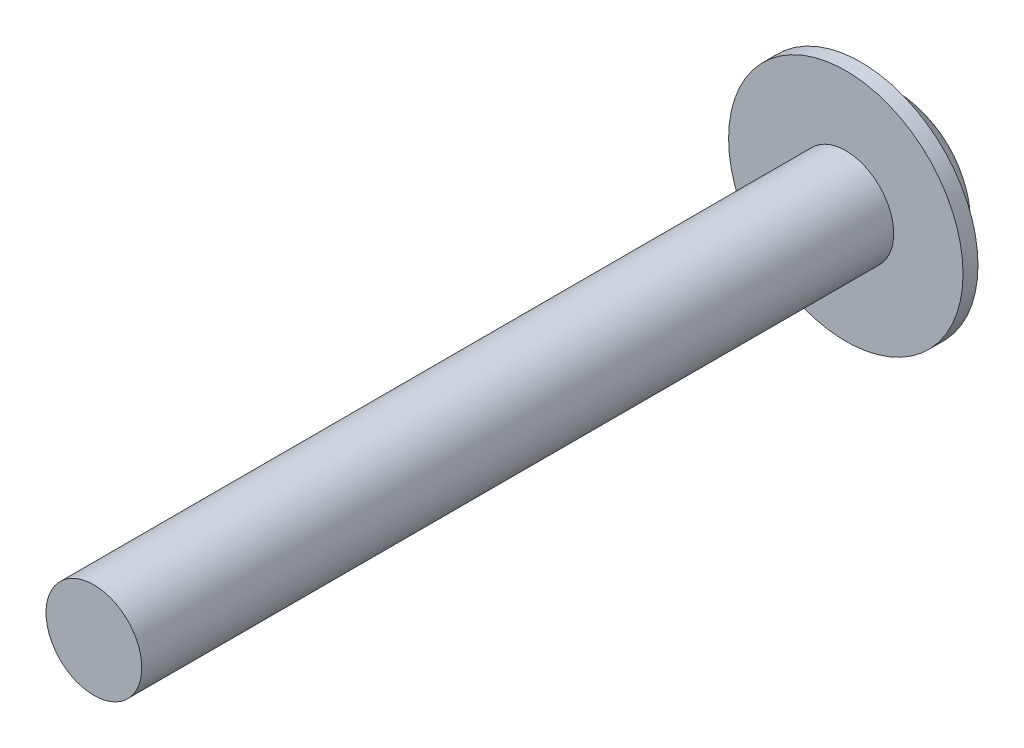
SolidWorks part; units mm, degrees
material "Chrome Stainless Steel"
ref_plane "Front Plane" through (0, 0, 0) normal (0, 0, 1) x (1, 0, 0)
ref_plane "Top Plane" through (0, 0, 0) normal (0, 1, 0) x (1, 0, 0)
ref_plane "Right Plane" through (0, 0, 0) normal (1, 0, 0) x (0, 0, -1)
sketch "Sketch1" plane through (0, 0, 0) normal (0, 0, 1) x (1, 0, 0)
  circle A0 centre (0, 0) radius 1.2192
  dimension "D1" = 2.4384
extrude "Extrude1" add sketch "Sketch1" along normal blind 19.144
sketch "Sketch2" plane through (0, 0, 0) normal (0, 0, -1) x (-1, 0, 0)
  circle A0 centre (0, 0) radius 2.9845
  dimension "D1" = 5.969
extrude "Extrude2" add sketch "Sketch2" along normal blind 0.381
sketch "Sketch3" plane through (0, 0, -0.381) normal (0, 0, -1) x (-1, 0, 0)
  circle A0 centre (0, 0) radius 2.2479
  dimension "D1" = 4.4958
extrude "Extrude3" add sketch "Sketch3" along normal blind 1.143
fillet "Fillet1" radius 1.016 1 edges at (-2.2479, 0, -1.524)
